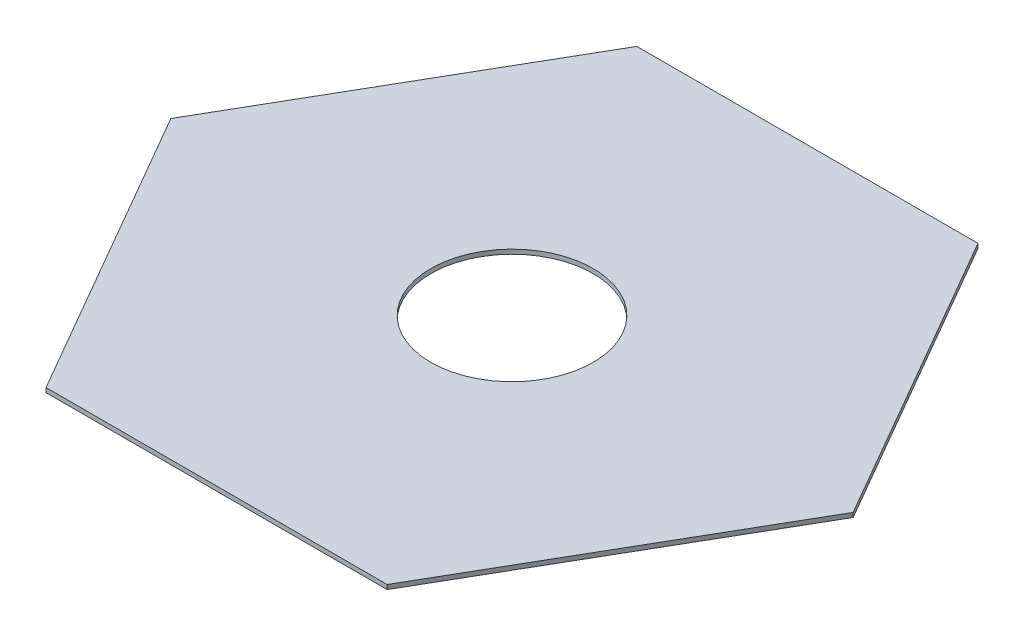
SolidWorks part; units mm, degrees
material "Thornel Mat VMA"
ref_plane "Alzado" through (0, 0, 0) normal (0, 0, 1) x (1, 0, 0)
ref_plane "Planta" through (0, 0, 0) normal (0, 1, 0) x (1, 0, 0)
ref_plane "Vista lateral" through (0, 0, 0) normal (1, 0, 0) x (0, 0, -1)
sketch "Croquis1" plane through (0, 0, 0) normal (0, 1, 0) x (1, 0, 0)
  line L1 (115.4701, -200) -> (230.9401, 0)
  line L2 (230.9401, 0) -> (115.4701, 200)
  line L3 (115.4701, 200) -> (-115.4701, 200)
  line L4 (-115.4701, 200) -> (-230.9401, 0)
  line L5 (-230.9401, 0) -> (-115.4701, -200)
  line L6 (-115.4701, -200) -> (115.4701, -200)
  circle A0 centre (0, 0) radius 200 construction
  circle A1 centre (0, 0) radius 55
  dimension "D2" = 110
  dimension "D1" = 400
extrude "Saliente-Extruir1" add sketch "Croquis1" along normal blind 3
